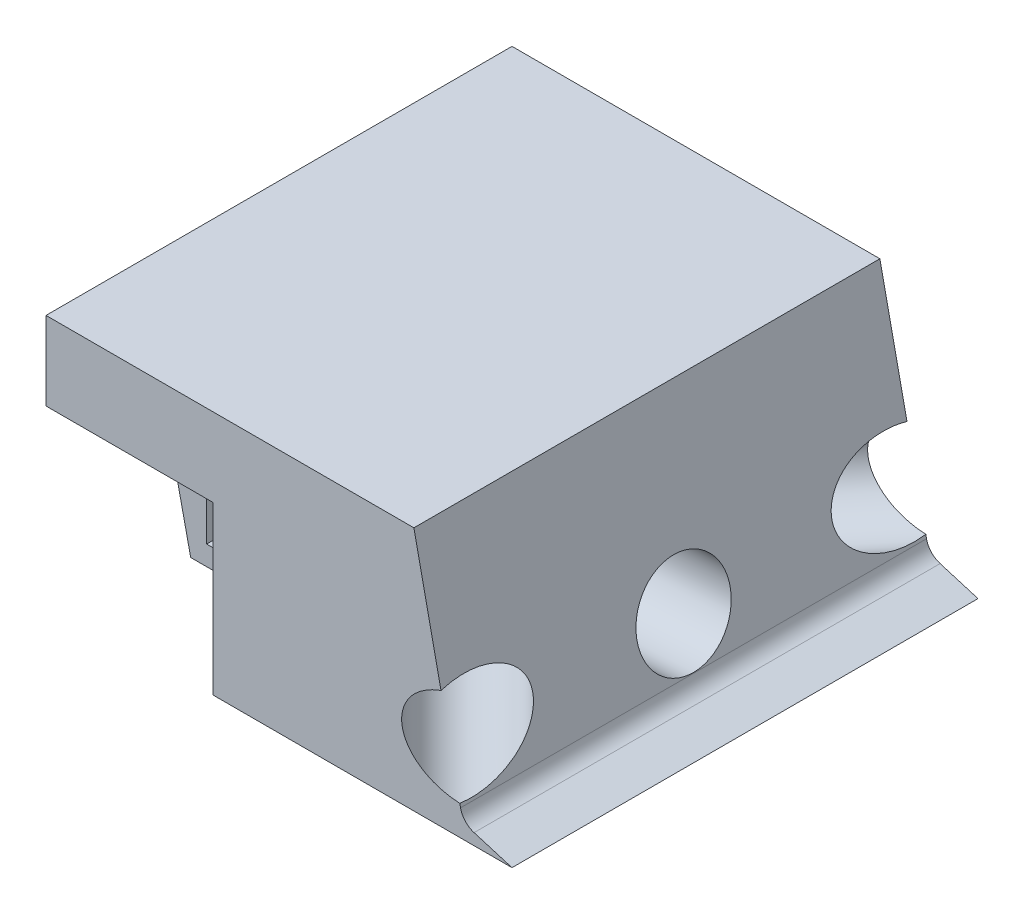
SolidWorks part; units mm, degrees
ref_plane "Front Plane" through (0, 0, 0) normal (0, 0, 1) x (1, 0, 0)
ref_plane "Top Plane" through (0, 0, 0) normal (0, 1, 0) x (1, 0, 0)
ref_plane "Right Plane" through (0, 0, 0) normal (1, 0, 0) x (0, 0, -1)
sketch "Sketch1" plane through (0, 0, 0) normal (0, 1, 0) x (1, 0, 0)
  line L1 (-55.9466, 49.5438) -> (39.0534, 49.5438)
  line L2 (-55.9466, 49.5438) -> (-55.9466, -45.4562)
  line L3 (-55.9466, -45.4562) -> (39.0534, -45.4562)
  line L4 (39.0534, 49.5438) -> (39.0534, -45.4562)
  dimension "D1" = 95
  dimension "D2" = 95
extrude "Boss-Extrude1" add sketch "Sketch1" along normal blind 50
sketch "Sketch2" plane through (0, 0, 45.4562) normal (0, 0, 1) x (1, 0, 0)
  line L0 (39.0534, 0) -> (36.3534, 50)
  line L1 (-55.9466, 50) -> (39.0534, 50) construction
  line L2 (36.3534, 50) -> (39.0534, 50)
  line L3 (39.0534, 50) -> (39.0534, 0)
  dimension "D1" = 2.7
extrude "Cut-Extrude1" cut sketch "Sketch2" against normal blind 100
sketch "Sketch3" plane through (38.9399, 2.1028, 0) normal (0.9985, 0.0539, 0) x (0, 0, -1)
  line L0 (-45.4562, 47.967) -> (-45.4562, -2.1058) construction
  line L1 (-45.4562, -2.1058) -> (49.5438, -2.1058) construction
  circle A0 centre (2.0438, 13.3942) radius 9.5
  point P4 (2.0438, -2.1058)
  dimension "D3" = 19
  dimension "D1" = 47.5
  dimension "D2" = 15.5
extrude "Cut-Extrude2" cut sketch "Sketch3" against normal blind 45
sketch "Sketch5" plane through (0, 50, 0) normal (0, 1, 0) x (1, 0, 0)
  line L0 (39.0534, 49.5438) -> (39.0534, 29.5438)
  line L1 (39.0534, -45.4562) -> (39.0534, 49.5438) construction
  line L2 (39.0534, 29.5438) -> (19.0534, 49.5438)
  line L3 (19.0534, 49.5438) -> (39.0534, 49.5438)
  line L4 (39.0534, -45.4562) -> (39.0534, -25.4562)
  line L5 (39.0534, -25.4562) -> (19.0534, -45.4562)
  line L6 (-55.9466, -45.4562) -> (36.3534, -45.4562) construction
  line L7 (19.0534, -45.4562) -> (39.0534, -45.4562)
  dimension "D1" = 20
  dimension "D2" = 20
  dimension "D3" = 20
  dimension "D4" = 20
extrude "Cut-Extrude4" cut sketch "Sketch5" against normal blind 45
sketch "Sketch6" plane through (0, 50, 0) normal (0, 1, 0) x (1, 0, 0)
  line L0 (19.0534, -45.4562) -> (12.9256, -39.3283)
  line L1 (12.9256, -39.3283) -> (6.7977, -45.4562)
  line L2 (-55.9466, -45.4562) -> (19.0534, -45.4562) construction
  line L3 (6.7977, -45.4562) -> (19.0534, -45.4562)
  line L4 (19.0534, 49.5438) -> (12.9256, 43.4159)
  line L5 (12.9256, 43.4159) -> (6.7977, 49.5438)
  line L6 (19.0534, 49.5438) -> (-55.9466, 49.5438) construction
  line L7 (6.7977, 49.5438) -> (19.0534, 49.5438)
extrude "Cut-Extrude5" cut sketch "Sketch6" against normal blind 45
sketch "Sketch7" plane through (-13.2014, 0, 13.2014) normal (-0.7071, 0, 0.7071) x (0.7071, 0, 0.7071)
  line L0 (45.6152, 5) -> (42.9152, 50)
  line L1 (45.6152, 50) -> (36.9491, 50) construction
  line L2 (42.9152, 50) -> (45.6152, 50)
  line L3 (45.6152, 50) -> (45.6152, 5)
  dimension "D1" = 2.7
extrude "Cut-Extrude6" cut sketch "Sketch7" against normal blind 45
sketch "Sketch8" plane through (-15.2452, 0, -15.2452) normal (-0.7071, 0, -0.7071) x (-0.7071, 0, 0.7071)
  line L0 (-48.5056, 5) -> (-45.8056, 50)
  line L1 (-39.8395, 50) -> (-48.5056, 50) construction
  line L2 (-45.8056, 50) -> (-48.5056, 50)
  line L3 (-48.5056, 50) -> (-48.5056, 5)
  dimension "D1" = 2.7
extrude "Cut-Extrude7" cut sketch "Sketch8" against normal blind 45
sketch "Sketch9" plane through (34.387, 2.9178, -34.387) normal (0.7058, 0.0599, -0.7058) x (-0.7084, 0.0597, -0.7033)
  line L1 (-6.2064, 2.4614) -> (-2.7761, 47.4176) construction
  line L2 (7.1802, -4.1889) -> (74.4757, -4.1889) construction
  circle A0 centre (14.527, 11.3111) radius 9.5
  point P6 (7.9302, 14.2331)
  dimension "D1" = 15.5
  dimension "D2" = 20
extrude "Cut-Extrude9" cut sketch "Sketch9" against normal blind 45
sketch "Sketch11" plane through (32.3505, 2.745, 32.3505) normal (0.7058, 0.0599, 0.7058) x (0.7033, 0.0597, -0.7084)
  line L0 (11.3114, 46.7473) -> (9.3514, 1.703) construction
  line L1 (-71.5478, 4.7302) -> (-4.7333, -3.3019) construction
  circle A0 centre (-10.1775, 12.9642) radius 9.5
  dimension "D1" = 20
  dimension "D2" = 15.5
extrude "Cut-Extrude10" cut sketch "Sketch11" against normal blind 45
sketch "Sketch12" plane through (0, 5, 0) normal (0, 1, 0) x (1, 0, 0)
  line L1 (38.7834, -45.4562) -> (6.7977, -45.4562)
  line L2 (38.7834, -45.4562) -> (38.7834, 49.5438)
  line L3 (38.7834, 49.5438) -> (6.7977, 49.5438)
  line L4 (6.7977, -45.4562) -> (6.7977, 49.5438)
extrude "Boss-Extrude2" add sketch "Sketch12" along normal blind 45
sketch "Sketch13" plane through (0, 0, 45.4562) normal (0, 0, 1) x (1, 0, 0)
  line L0 (39.0534, 0) -> (29.0534, 3)
  line L1 (29.0534, 3) -> (19.0534, 50)
  line L2 (-55.9466, 50) -> (38.7834, 50) construction
  line L3 (19.0534, 50) -> (49.7453, 50)
  line L4 (49.7453, 50) -> (39.0534, 0)
  line L5 (-55.9466, 0) -> (39.0534, 0) construction
  dimension "D1" = 10
  dimension "D2" = 3
  dimension "D3" = 10
extrude "Cut-Extrude11" cut sketch "Sketch13" against normal blind 100
sketch "Sketch14" plane through (-5.9946, -0.3237, 0) normal (0.9985, 0.0539, 0) x (0, 0, -1)
  circle A0 centre (2.0438, 13.3942) radius 9.5
extrude "Cut-Extrude12" cut sketch "Sketch14" along normal blind 100
sketch "Sketch15" plane through (0.5878, 0.0499, 0.5878) normal (0.7058, 0.0599, 0.7058) x (0.7033, 0.0597, -0.7084)
  circle A0 centre (-10.1775, 12.9642) radius 9.5
extrude "Cut-Extrude13" cut sketch "Sketch15" along normal blind 100
sketch "Sketch16" plane through (2.6243, 0.2227, -2.6243) normal (0.7058, 0.0599, -0.7058) x (-0.7084, 0.0597, -0.7033)
  circle A0 centre (14.527, 11.3111) radius 9.5
extrude "Cut-Extrude14" cut sketch "Sketch16" along normal blind 100
fillet "Fillet2" radius 4 1 edges at (29.0534, 3, -2.0438)
sketch "Sketch17" plane through (0, 0, 45.4562) normal (0, 0, 1) x (1, 0, 0)
  line L3 (-55.9466, 0) -> (-21.9466, 0)
  line L4 (-55.9466, 0) -> (-55.9466, 34)
  line L5 (-55.9466, 34) -> (-21.9466, 34)
  line L6 (-21.9466, 0) -> (-21.9466, 34)
  dimension "D1" = 34
  dimension "D2" = 34
extrude "Cut-Extrude16" cut sketch "Sketch17" against normal blind 22
sketch "Sketch19" plane through (0, 0, -49.5438) normal (0, 0, -1) x (-1, 0, 0)
  line L1 (55.9466, 0) -> (21.9466, 0)
  line L2 (55.9466, 0) -> (55.9466, 34)
  line L3 (55.9466, 34) -> (21.9466, 34)
  line L4 (21.9466, 0) -> (21.9466, 34)
  dimension "D1" = 34
  dimension "D2" = 34
extrude "Cut-Extrude17" cut sketch "Sketch19" against normal blind 22
sketch "Sketch20" plane through (0, 0, 23.4562) normal (0, 0, 1) x (1, 0, 0)
  line L0 (-55.9466, 0) -> (-21.9466, 0) construction
  line L1 (-45.1966, 20.5) -> (-32.6966, 20.5)
  line L2 (-45.1966, 20.5) -> (-45.1966, 4)
  line L3 (-45.1966, 4) -> (-32.6966, 4)
  line L4 (-32.6966, 20.5) -> (-32.6966, 4)
  line L5 (-55.9466, 34) -> (-55.9466, 0) construction
  line L6 (-21.9466, 0) -> (-21.9466, 34) construction
  dimension "D1" = 12.5
  dimension "D2" = 16.5
  dimension "D3" = 4
  dimension "D4" = 10.75
  dimension "D5" = 10.75
extrude "Cut-Extrude18" cut sketch "Sketch20" against normal blind 60
sketch "Sketch21" plane through (0, 0, 23.4562) normal (0, 0, 1) x (1, 0, 0)
  line L0 (-55.9466, 34) -> (-48.4466, 0)
  line L1 (-55.9466, 0) -> (-21.9466, 0) construction
  line L2 (-48.4466, 0) -> (-55.9466, 0)
  line L3 (-55.9466, 0) -> (-55.9466, 34)
  dimension "D1" = 7.5
extrude "Cut-Extrude19" cut sketch "Sketch21" against normal blind 60
